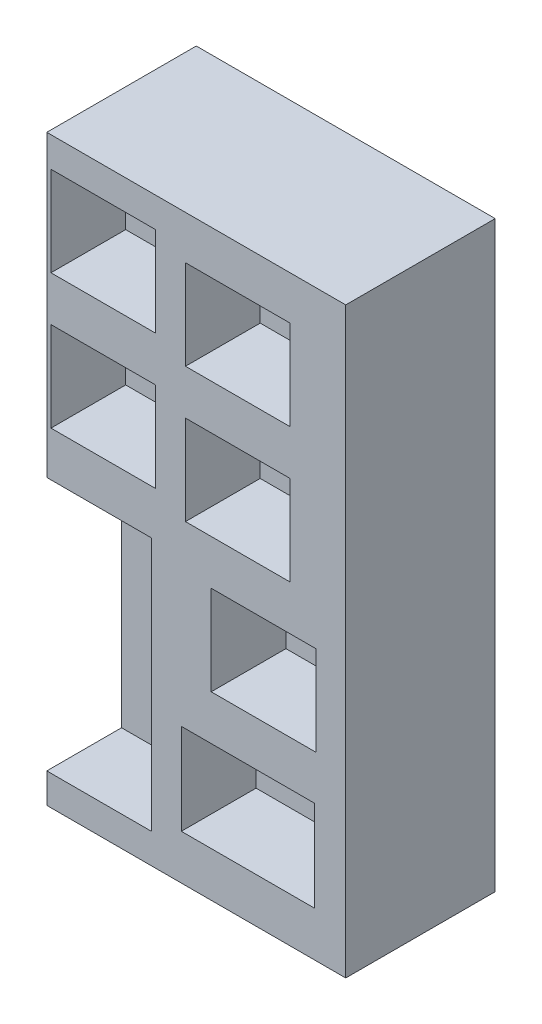
SolidWorks part; units mm, degrees
ref_plane "Front" through (0, 0, 0) normal (0, 0, 1) x (1, 0, 0)
ref_plane "Top" through (0, 0, 0) normal (0, 1, 0) x (1, 0, 0)
ref_plane "Right" through (0, 0, 0) normal (1, 0, 0) x (0, 0, -1)
sketch "Sketch1" plane through (0, 0, 0) normal (0, 0, 1) x (1, 0, 0)
  line L1 (-27.8641, 26.3351) -> (-2.4641, 26.3351)
  line L2 (-27.8641, 26.3351) -> (-27.8641, -23.1949)
  line L3 (-27.8641, -23.1949) -> (-2.4641, -23.1949)
  line L4 (-2.4641, 26.3351) -> (-2.4641, -23.1949)
  dimension "D1" = 25.4
  dimension "D2" = 49.53
extrude "Boss-Extrude2" add sketch "Sketch1" along normal blind 12.7
sketch "Sketch2" plane through (0, 0, 12.7) normal (0, 0, 1) x (1, 0, 0)
  line L0 (-27.8641, -23.1949) -> (-2.4641, -23.1949) construction
  line L1 (-27.8641, 0.9351) -> (-18.9741, 0.9351)
  line L2 (-27.8641, 0.9351) -> (-27.8641, -20.6549)
  line L3 (-27.8641, -20.6549) -> (-18.9741, -20.6549)
  line L4 (-18.9741, 0.9351) -> (-18.9741, -20.6549)
  line L5 (-27.8641, 26.3351) -> (-27.8641, -23.1949) construction
  line L6 (-2.4641, -23.1949) -> (-2.4641, 26.3351) construction
  line L7 (-2.4641, 26.3351) -> (-27.8641, 26.3351) construction
  line L9 (-16.4341, -19.3849) -> (-5.1099, -19.3849)
  line L10 (-16.4341, -19.3849) -> (-16.4341, -11.6601)
  line L11 (-16.4341, -11.6601) -> (-5.1099, -11.6601)
  line L12 (-5.1099, -19.3849) -> (-5.1099, -11.6601)
  line L13 (-13.8941, -7.8501) -> (-5.0041, -7.8501)
  line L14 (-13.8941, -7.8501) -> (-13.8941, -0.2301)
  line L15 (-13.8941, -0.2301) -> (-5.0041, -0.2301)
  line L16 (-5.0041, -7.8501) -> (-5.0041, -0.2301)
  line L17 (-27.5113, 4.7451) -> (-18.6213, 4.7451)
  line L18 (-27.5113, 4.7451) -> (-27.5113, 12.3651)
  line L19 (-27.5113, 12.3651) -> (-18.6213, 12.3651)
  line L20 (-18.6213, 4.7451) -> (-18.6213, 12.3651)
  line L21 (-16.0813, 3.5799) -> (-7.1913, 3.5799)
  line L22 (-16.0813, 3.5799) -> (-16.0813, 11.1999)
  line L23 (-16.0813, 11.1999) -> (-7.1913, 11.1999)
  line L24 (-7.1913, 3.5799) -> (-7.1913, 11.1999)
  line L25 (-27.5113, 16.1751) -> (-18.6213, 16.1751)
  line L26 (-27.5113, 16.1751) -> (-27.5113, 23.7951)
  line L27 (-27.5113, 23.7951) -> (-18.6213, 23.7951)
  line L28 (-18.6213, 16.1751) -> (-18.6213, 23.7951)
  line L29 (-16.0813, 22.6299) -> (-7.1913, 22.6299)
  line L30 (-16.0813, 22.6299) -> (-16.0813, 15.0099)
  line L31 (-16.0813, 15.0099) -> (-7.1913, 15.0099)
  line L32 (-7.1913, 22.6299) -> (-7.1913, 15.0099)
  dimension "D1" = 8.89
  dimension "D2" = 21.59
  dimension "D3" = 2.54
  dimension "D4" = 3.81
  dimension "D5" = 2.6458
  dimension "D6" = 2.54
  dimension "D7" = 7.7248
  dimension "D8" = 3.81
  dimension "D9" = 7.62
  dimension "D10" = 7.62
  dimension "D11" = 3.81
  dimension "D12" = 8.89
  dimension "D13" = 3.81
  dimension "D14" = 8.89
  dimension "D16" = 8.89
  dimension "D17" = 2.54
  dimension "D18" = 2.54
  dimension "D19" = 3.81
  dimension "D20" = 7.62
  dimension "D21" = 2.54
  dimension "D22" = 2.54
  dimension "D23" = 3.81
  dimension "D24" = 8.89
  dimension "D25" = 7.62
  dimension "D26" = 7.62
  dimension "D27" = 3.7052
  dimension "D28" = 2.54
extrude "Cut-Extrude1" cut sketch "Sketch2" against normal blind 6.35
